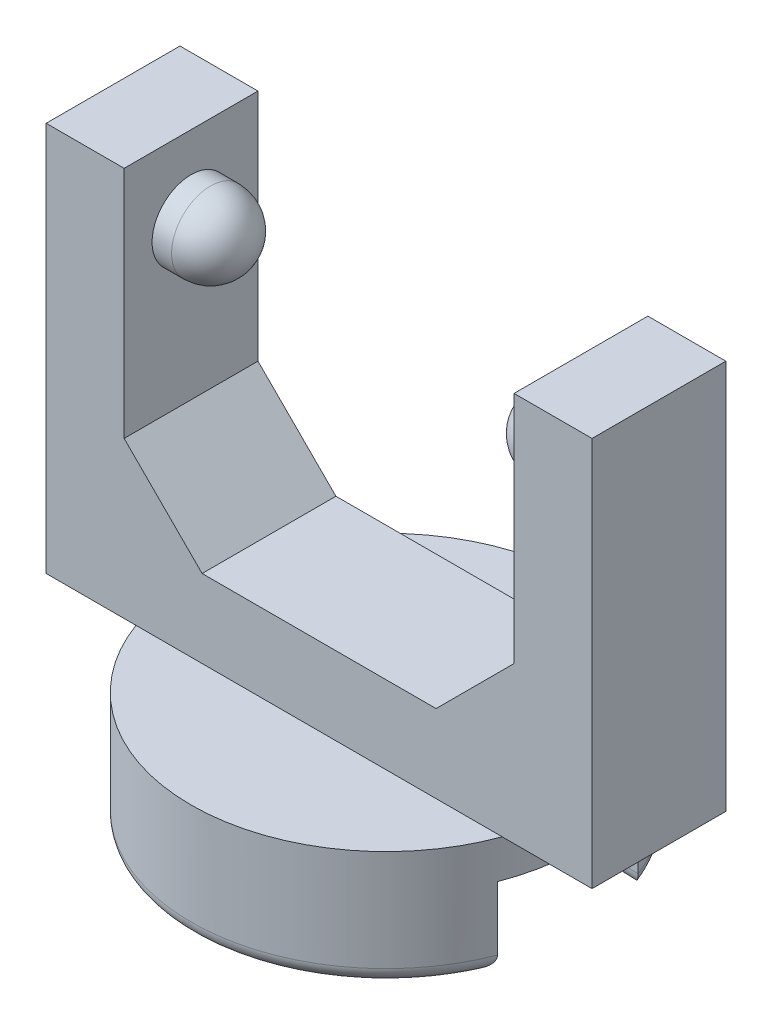
SolidWorks part; units mm, degrees
ref_plane "Front Plane" through (0, 0, 0) normal (0, 0, 1) x (1, 0, 0)
ref_plane "Top Plane" through (0, 0, 0) normal (0, 1, 0) x (1, 0, 0)
ref_plane "Right Plane" through (0, 0, 0) normal (1, 0, 0) x (0, 0, -1)
sketch "Sketch1" plane through (0, 0, 0) normal (0, 1, 0) x (1, 0, 0)
  circle A0 centre (0, 0) radius 12.5
  dimension "D1" = 25
extrude "Boss-Extrude1" add sketch "Sketch1" along normal blind 7.5
sketch "Sketch2" plane through (0, 7.5, 0) normal (0, 1, 0) x (1, 0, 0)
  line L1 (-17.5, 4.2904) -> (17.5, 4.2904)
  line L2 (-17.5, 4.2904) -> (-17.5, -4.2904)
  line L3 (-17.5, -4.2904) -> (17.5, -4.2904)
  line L4 (17.5, 4.2904) -> (17.5, -4.2904)
  point P4 (17.5, 0)
  point P6 (0, 4.2904)
  dimension "D1" = 35
  dimension "D3" = 8.5808
extrude "Boss-Extrude2" add sketch "Sketch2" along normal blind 25
sketch "Sketch3" plane through (0, 32.5, 0) normal (0, 1, 0) x (1, 0, 0)
  line L0 (17.5, 4.2904) -> (-17.5, 4.2904) construction
  line L1 (-12.5, 4.2904) -> (12.5, 4.2904)
  line L2 (-12.5, 4.2904) -> (-12.5, -4.2904)
  line L3 (-12.5, -4.2904) -> (12.5, -4.2904)
  line L4 (12.5, 4.2904) -> (12.5, -4.2904)
  line L5 (-17.5, -4.2904) -> (17.5, -4.2904) construction
  line L6 (17.5, -4.2904) -> (17.5, 4.2904) construction
  line L7 (-17.5, 4.2904) -> (-17.5, -4.2904) construction
  dimension "D1" = 5
  dimension "D2" = 5
extrude "Cut-Extrude1" cut sketch "Sketch3" against normal blind 20
sketch "Sketch4" plane through (-12.5, 0, 0) normal (1, 0, 0) x (0, 0, -1)
  line L0 (4.2904, 12.5) -> (-4.2904, 12.5) construction
  line L1 (4.2904, 32.5) -> (-4.2904, 32.5) construction
  circle A0 centre (0, 27.5) radius 2.5
  point P8 (0, 32.5)
  dimension "D1" = 5
  dimension "D2" = 15
extrude "Boss-Extrude3" add sketch "Sketch4" along normal blind 3.75
sketch "Sketch5" plane through (12.5, 0, 0) normal (-1, 0, 0) x (0, 0, 1)
  circle A0 centre (0, 27.5) radius 2.5
  circle A1 centre (0, 27.5) radius 2.5 construction
  dimension "D1" = 5
extrude "Boss-Extrude4" add sketch "Sketch5" along normal blind 3.75
fillet "Fillet2" radius 2.5 1 edges at (-8.75, 27.5, -2.5)
fillet "Fillet3" radius 2.5 1 edges at (8.75, 27.5, 2.5)
chamfer "Chamfer1" distance 5 angle 45 1 edges at (-12.5, 12.5, 0)
chamfer "Chamfer2" distance 5 angle 45 1 edges at (12.5, 12.5, 0)
sketch "Sketch6" plane through (0, 0, 0) normal (0, -1, 0) x (1, 0, 0)
  line L0 (11.6578, -4.5105) -> (7.751, -4.6549)
  line L1 (7.751, -4.6549) -> (-0.1865, -9.2376)
  line L2 (-0.1865, -9.2376) -> (-8.124, -4.6549)
  line L3 (-8.124, -4.6549) -> (-8.124, 4.5105)
  line L4 (-8.124, 4.5105) -> (-0.1865, 9.0933)
  line L5 (-0.1865, 9.0933) -> (7.751, 4.5105)
  line L6 (7.751, 4.5105) -> (11.6578, 4.5105)
  circle A0 centre (0, 0) radius 12.5
  arc A1 (11.6578, 4.5105) -> (11.6578, -4.5105) centre (0, 0) ccw
  circle A2 centre (0, 0) radius 12.5 construction
  circle M1 centre (0, 0) radius 12.5
extrude "Cut-Extrude2" cut sketch "Sketch6" against normal blind 5.08 contours L6 L5 L4 L3 L2 L1 L0 M1
fillet "Fillet4" radius 1 8 edges at (3.7822, 0, 6.8019) (-4.1553, 0, 6.8019) (-8.124, 0, -0.0722) (-4.1553, 0, -6.9462) (3.7822, 0, -6.9462) (9.7044, 0, -4.5827) (-12.5, 0, 0) (9.7044, 0, 4.5105)
